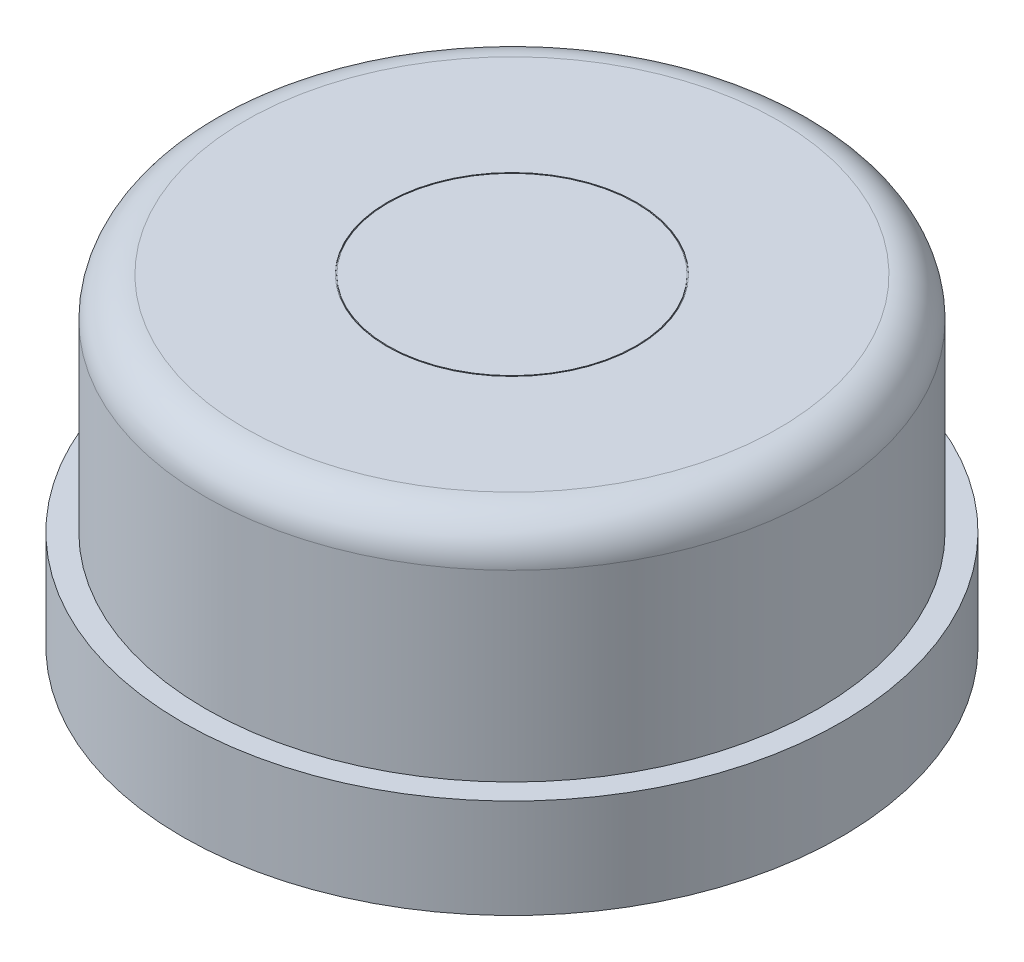
SolidWorks part; units mm, degrees
ref_plane "Front" through (0, 0, 0) normal (0, 0, 1) x (1, 0, 0)
ref_plane "Top" through (0, 0, 0) normal (0, 1, 0) x (1, 0, 0)
ref_plane "Right" through (0, 0, 0) normal (1, 0, 0) x (0, 0, -1)
sketch "Sketch1" plane through (0, 0, 0) normal (0, 1, 0) x (1, 0, 0)
  circle A0 centre (0, 0) radius 8.4455
  dimension "D1" = 16.891
extrude "Boss-Extrude1" add sketch "Sketch1" along normal blind 2.54
sketch "Sketch2" plane through (0, 0, 0) normal (0, 1, 0) x (1, 0, 0)
  circle A0 centre (0, 0) radius 7.8486
  dimension "D1" = 15.6972
extrude "Boss-Extrude2" add sketch "Sketch2" along normal blind 8.255
fillet "Fillet1" radius 1.016 1 edges at (0, 8.255, 7.8486)
sketch "Sketch3" plane through (0, 8.255, 0) normal (0, 1, 0) x (1, 0, 0)
  circle A0 centre (0, 0) radius 3.175
  dimension "D1" = 6.35
extrude "Cut-Extrude-Thin1" cut sketch "Sketch3" against normal blind 0.0254 thin
